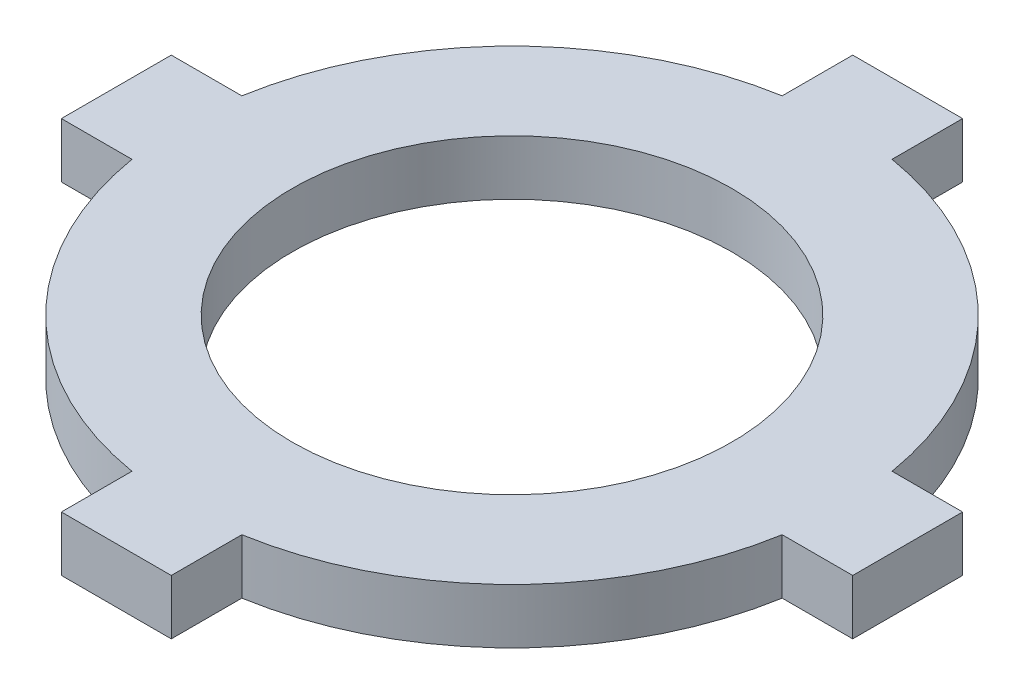
SolidWorks part; units mm, degrees
ref_plane "Front Plane" through (0, 0, 0) normal (0, 0, 1) x (1, 0, 0)
ref_plane "Top Plane" through (0, 0, 0) normal (0, 1, 0) x (1, 0, 0)
ref_plane "Right Plane" through (0, 0, 0) normal (1, 0, 0) x (0, 0, -1)
sketch "Sketch1" plane through (0, 0, 0) normal (0, 1, 0) x (1, 0, 0)
  line L5 (-18.7836, -3.175) -> (-22.86, -3.175)
  line L6 (22.86, -3.175) -> (18.7836, -3.175)
  line L18 (22.86, -3.175) -> (22.86, 3.175)
  line L19 (22.86, 3.175) -> (18.7836, 3.175)
  line L29 (-22.86, -3.175) -> (-22.86, 3.175)
  line L32 (3.175, -22.86) -> (-3.175, -22.86)
  line L33 (3.175, -22.86) -> (3.175, -18.7836)
  line L34 (3.175, 22.86) -> (-3.175, 22.86)
  line L35 (-3.175, -22.86) -> (-3.175, -18.7836)
  line L46 (3.175, 18.7836) -> (3.175, 22.86)
  line L49 (-3.175, 18.7836) -> (-3.175, 22.86)
  line L50 (-18.7836, 3.175) -> (-22.86, 3.175)
  circle A18 centre (0, 0) radius 12.7
  arc A19 (-18.7836, -3.175) -> (-3.175, -18.7836) centre (0, 0) ccw
  arc A20 (-3.175, 18.7836) -> (-18.7836, 3.175) centre (0, 0) ccw
  arc A21 (18.7836, 3.175) -> (3.175, 18.7836) centre (0, 0) ccw
  arc A22 (3.175, -18.7836) -> (18.7836, -3.175) centre (0, 0) ccw
  dimension "D4" = 45.72
  dimension "D5" = 45.72
  dimension "D6" = 6.35
  dimension "D2" = 25.4
  dimension "D3" = 6.35
extrude "Boss-Extrude1" add sketch "Sketch1" along normal blind 3.175
